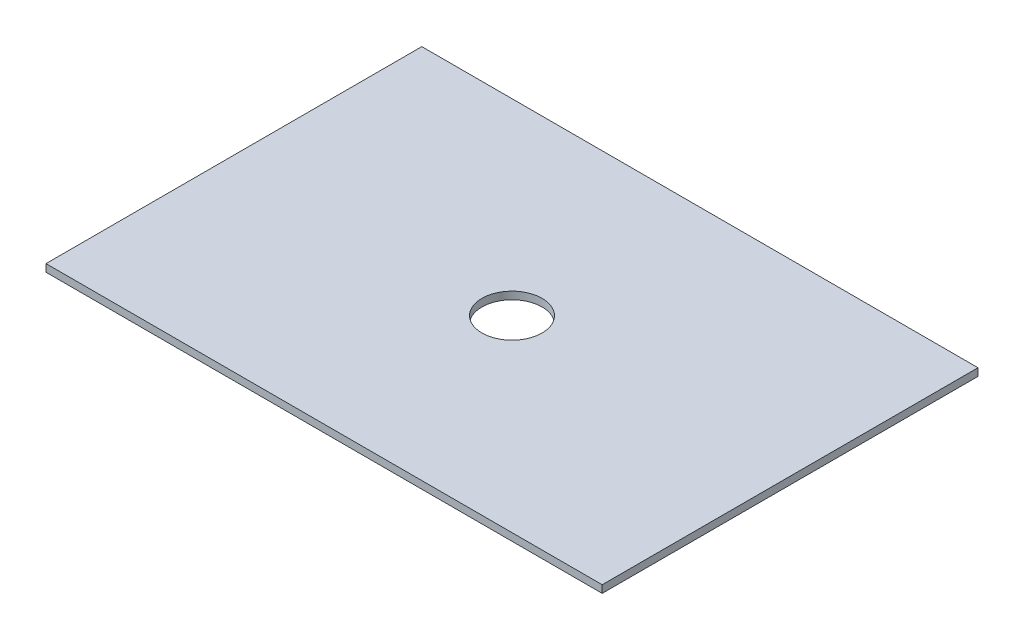
SolidWorks part; units mm, degrees
material "Acrylic (Medium-high impact)"
ref_plane "Front Plane" through (0, 0, 0) normal (0, 0, 1) x (1, 0, 0)
ref_plane "Top Plane" through (0, 0, 0) normal (0, 1, 0) x (1, 0, 0)
ref_plane "Right Plane" through (0, 0, 0) normal (1, 0, 0) x (0, 0, -1)
sketch "Sketch1" plane through (0, 0, 0) normal (0, 1, 0) x (1, 0, 0)
  line L0 (234.95, 317.5) -> (234.95, 0) construction
  line L1 (0, 0) -> (469.9, 0)
  line L2 (0, 0) -> (0, 317.5)
  line L3 (0, 317.5) -> (469.9, 317.5)
  line L4 (469.9, 0) -> (469.9, 317.5)
  line L5 (0, 158.75) -> (469.9, 158.75) construction
  circle A0 centre (234.95, 158.75) radius 25.4
  dimension "D3" = 50.8
  dimension "D1" = 469.9
  dimension "D2" = 317.5
extrude "Boss-Extrude1" add sketch "Sketch1" along normal blind 6.35
